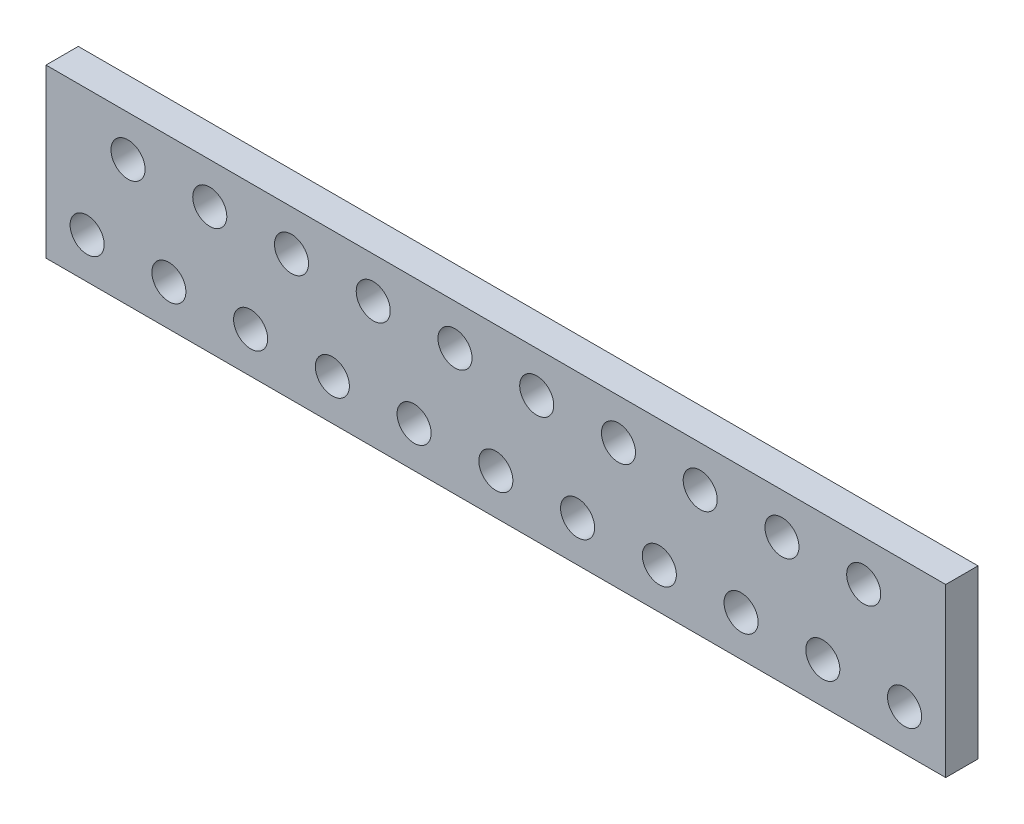
SolidWorks part; units mm, degrees
ref_plane "Front" through (0, 0, 0) normal (0, 0, 1) x (1, 0, 0)
ref_plane "Top" through (0, 0, 0) normal (0, 1, 0) x (1, 0, 0)
ref_plane "Right" through (0, 0, 0) normal (1, 0, 0) x (0, 0, -1)
sketch "Sketch1" plane through (0, 0, 0) normal (0, 0, 1) x (1, 0, 0)
  line L1 (-19.812, 3.683) -> (19.812, 3.683)
  line L2 (-19.812, 3.683) -> (-19.812, -3.683)
  line L3 (-19.812, -3.683) -> (19.812, -3.683)
  line L4 (19.812, 3.683) -> (19.812, -3.683)
extrude "PEEK" add sketch "Sketch1" along normal blind 1.4224 contours L1 L4 L3 L2
sketch "Sketch2" plane through (0, 0, 0) normal (0, 0, -1) x (-1, 0, 0)
  circle A0 centre (-18, -1.885) radius 0.75
  circle A1 centre (-14.4, -1.885) radius 0.75
  circle A2 centre (-10.8, -1.885) radius 0.75
  circle A3 centre (-7.2, -1.885) radius 0.75
  circle A4 centre (-3.6, -1.885) radius 0.75
  circle A5 centre (0, -1.885) radius 0.75
  circle A6 centre (3.6, -1.885) radius 0.75
  circle A7 centre (7.2, -1.885) radius 0.75
  circle A8 centre (10.8, -1.885) radius 0.75
  circle A9 centre (14.4, -1.885) radius 0.75
  circle A10 centre (18, -1.885) radius 0.75
  circle A11 centre (16.2, 1.885) radius 0.75
  circle A12 centre (12.6, 1.885) radius 0.75
  circle A13 centre (9, 1.885) radius 0.75
  circle A14 centre (5.4, 1.885) radius 0.75
  circle A15 centre (1.8, 1.885) radius 0.75
  circle A16 centre (-1.8, 1.885) radius 0.75
  circle A17 centre (-5.4, 1.885) radius 0.75
  circle A18 centre (-9, 1.885) radius 0.75
  circle A19 centre (-12.6, 1.885) radius 0.75
  circle A20 centre (-16.2, 1.885) radius 0.75
extrude "Cut-Extrude1" cut sketch "Sketch2" against normal through all
